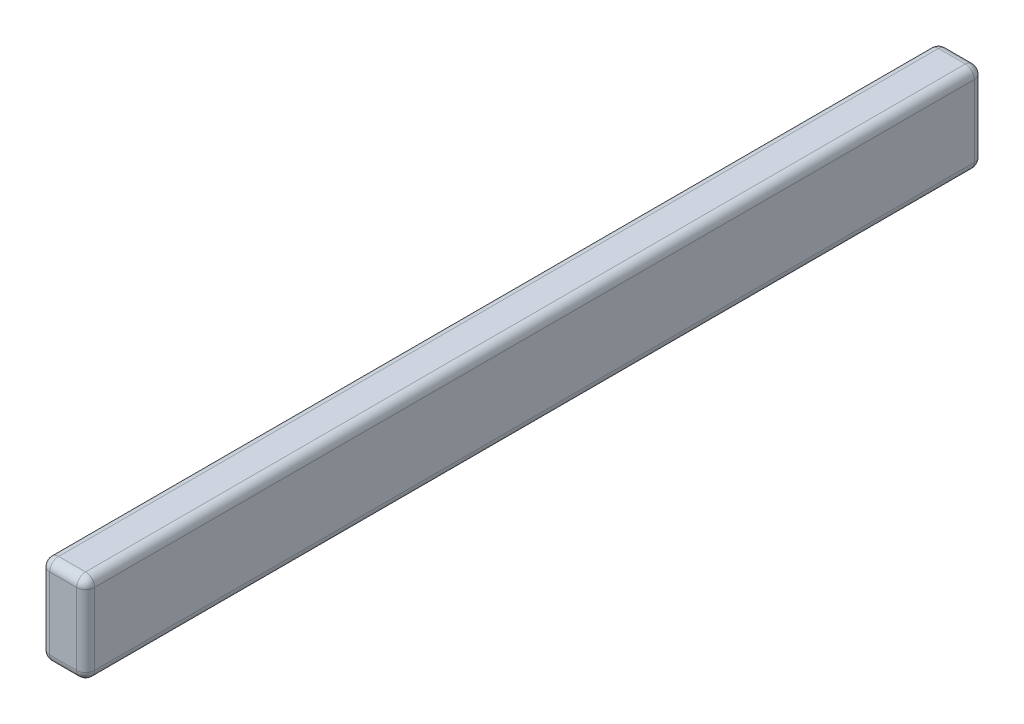
SolidWorks part; units mm, degrees
ref_plane "Plan de face" through (0, 0, 0) normal (0, 0, 1) x (1, 0, 0)
ref_plane "Plan de dessus" through (0, 0, 0) normal (0, 1, 0) x (1, 0, 0)
ref_plane "Plan de droite" through (0, 0, 0) normal (1, 0, 0) x (0, 0, -1)
sketch "Esquisse1" plane through (0, 0, 0) normal (0, 0, 1) x (1, 0, 0)
  line L1 (-28.2934, 24.9697) -> (21.7066, 24.9697)
  line L2 (-28.2934, 24.9697) -> (-28.2934, -75.0303)
  line L3 (-28.2934, -75.0303) -> (21.7066, -75.0303)
  line L4 (21.7066, 24.9697) -> (21.7066, -75.0303)
extrude "Boss.-Extru.1" add sketch "Esquisse1" along normal blind 1000 contours L1 L4 L3 L2
fillet "Congé1" radius 10 4 edges at (21.7066, 24.9697, 500) (-28.2934, 24.9697, 500) (21.7066, -75.0303, 500) (-28.2934, -75.0303, 500)
fillet "Congé2" radius 10 16 edges at (-25.3645, 22.0408, 1000) (-3.2934, 24.9697, 1000) (18.7776, 22.0408, 1000) (18.7776, -72.1013, 1000) (-3.2934, -75.0303, 1000) (-25.3645, -72.1013, 1000) (-25.3645, 22.0408, 0) (-3.2934, 24.9697, 0) (18.7776, 22.0408, 0) (18.7776, -72.1013, 0) (-3.2934, -75.0303, 0) (-25.3645, -72.1013, 0) (21.7066, -25.0303, 1000) (-28.2934, -25.0303, 1000) (21.7066, -25.0303, 0) (-28.2934, -25.0303, 0)
